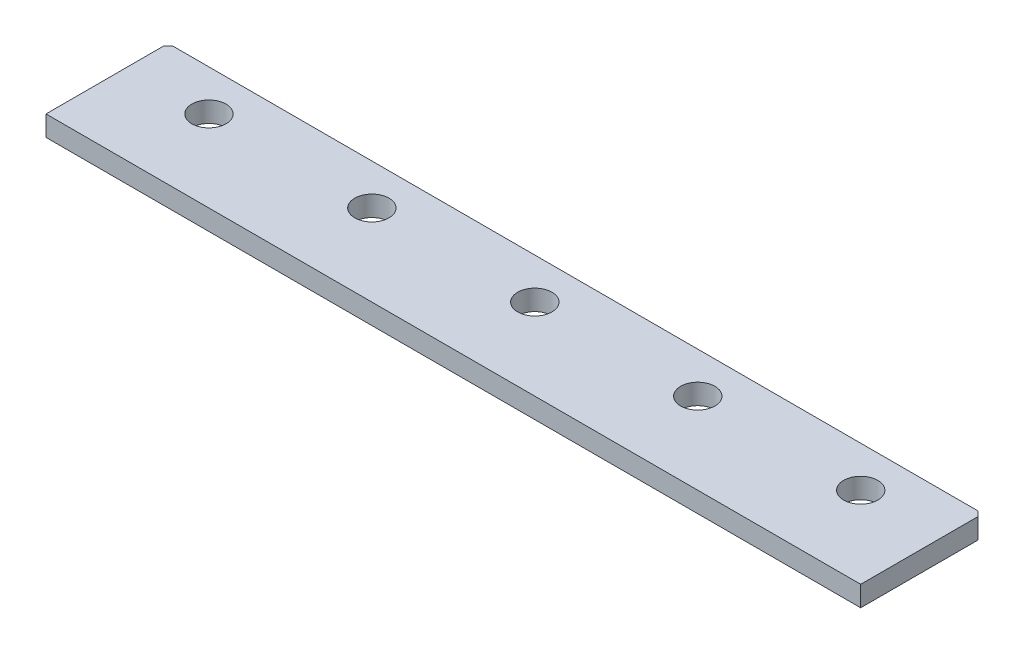
SolidWorks part; units mm, degrees
ref_plane "Front Plane" through (0, 0, 0) normal (0, 0, 1) x (1, 0, 0)
ref_plane "Top Plane" through (0, 0, 0) normal (0, 1, 0) x (1, 0, 0)
ref_plane "Right Plane" through (0, 0, 0) normal (1, 0, 0) x (0, 0, -1)
sketch "Sketch1" plane through (0, 0, 0) normal (0, 1, 0) x (1, 0, 0)
  line L1 (63.5, -9.525) -> (-63.5, -9.525)
  line L2 (63.5, -9.525) -> (63.5, 9.525)
  line L3 (63.5, 9.525) -> (-63.5, 9.525)
  line L4 (-63.5, -9.525) -> (-63.5, 9.525)
  line L5 (63.5, -9.525) -> (-63.5, 9.525) construction
  line L6 (63.5, 9.525) -> (-63.5, -9.525) construction
  point P0 (0, 0)
extrude "Boss-Extrude1" add sketch "Sketch1" along normal blind 3.175
sketch "Sketch2" plane through (0, 3.175, 0) normal (0, 1, 0) x (1, 0, 0)
  line L0 (63.5, 9.525) -> (63.5, 3.175)
  line L1 (63.5, -9.525) -> (63.5, 9.525) construction
  line L2 (63.5, 3.175) -> (50.8, 3.175)
  line L3 (38.1, 3.175) -> (25.4, 3.175)
  line L4 (12.7, 3.175) -> (0, 3.175)
  line L5 (-12.7, 3.175) -> (-25.4, 3.175)
  line L6 (-38.1, 3.175) -> (-50.8, 3.175)
  circle A0 centre (50.8, 3.175) radius 2.667
  circle A1 centre (25.4, 3.175) radius 2.667
  circle A2 centre (0, 3.175) radius 2.667
  circle A3 centre (-25.4, 3.175) radius 2.667
  circle A4 centre (-50.8, 3.175) radius 2.667
  dimension "D3" = 5
  dimension "D1" = 6.35
  dimension "D2" = 12.7
extrude "Cut-Extrude1" cut sketch "Sketch2" against normal blind 3.175
sketch "Sketch3" plane through (0, 3.175, 0) normal (0, 1, 0) x (1, 0, 0)
  line L0 (-63.5, 9.525) -> (-63.5, 8.763)
  line L1 (-63.5, 9.525) -> (-63.5, -9.525) construction
  line L2 (-63.5, 9.525) -> (-62.738, 9.525)
  line L3 (63.5, 9.525) -> (-63.5, 9.525) construction
  line L4 (-62.738, 9.525) -> (-63.5, 8.763)
  line L5 (63.5, 9.525) -> (63.5, 8.763)
  line L6 (63.5, -9.525) -> (63.5, 9.525) construction
  line L7 (63.5, 8.763) -> (62.738, 9.525)
  line L8 (62.738, 9.525) -> (63.5, 9.525)
  dimension "D2" = 0.762
  dimension "D1" = 0.762
  dimension "D3" = 0.762
extrude "Cut-Extrude2" cut sketch "Sketch3" against normal blind 3.175
